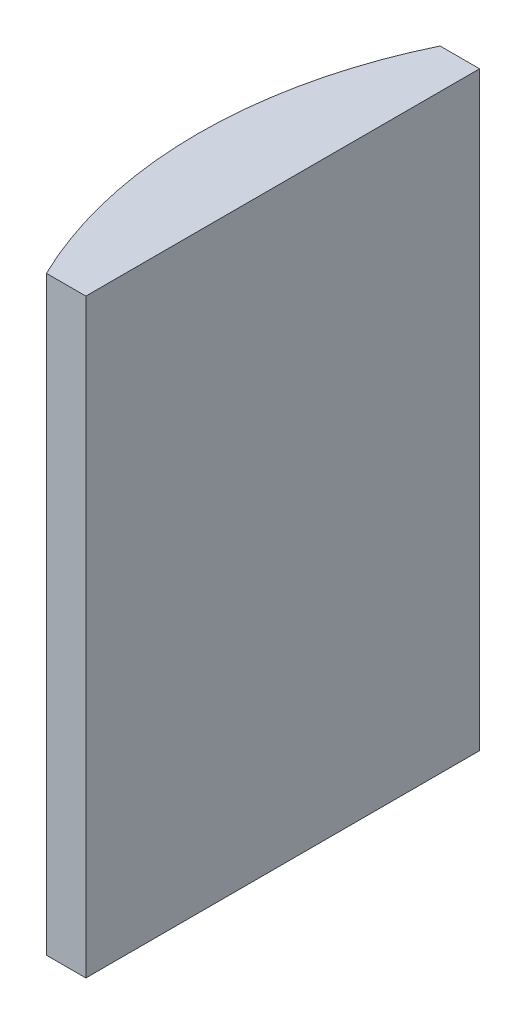
SolidWorks part; units mm, degrees
ref_plane "前视基准面" through (0, 0, 0) normal (0, 0, 1) x (1, 0, 0)
ref_plane "上视基准面" through (0, 0, 0) normal (0, 1, 0) x (1, 0, 0)
ref_plane "右视基准面" through (0, 0, 0) normal (1, 0, 0) x (0, 0, -1)
sketch "草图1" plane through (0, 0, 0) normal (0, 1, 0) x (1, 0, 0)
  line L0 (-137.6835, 0) -> (10.8051, 0) construction
  line L1 (-16.2682, 10) -> (-14.2648, 10)
  line L2 (-16.2682, -10) -> (-14.2648, -10)
  line L3 (-14.2648, 10) -> (-14.2648, -10)
  arc A0 (-16.2682, 10) -> (-16.2682, -10) centre (4.3552, 0) ccw
  point P2 (-18.5648, 0)
  point P4 (-14.2648, 0)
  dimension "D2" = 10
  dimension "D3" = 22.92
  dimension "D4" = 4.3
  dimension "D1" = 10
extrude "凸台-拉伸1" add sketch "草图1" along normal blind 30
